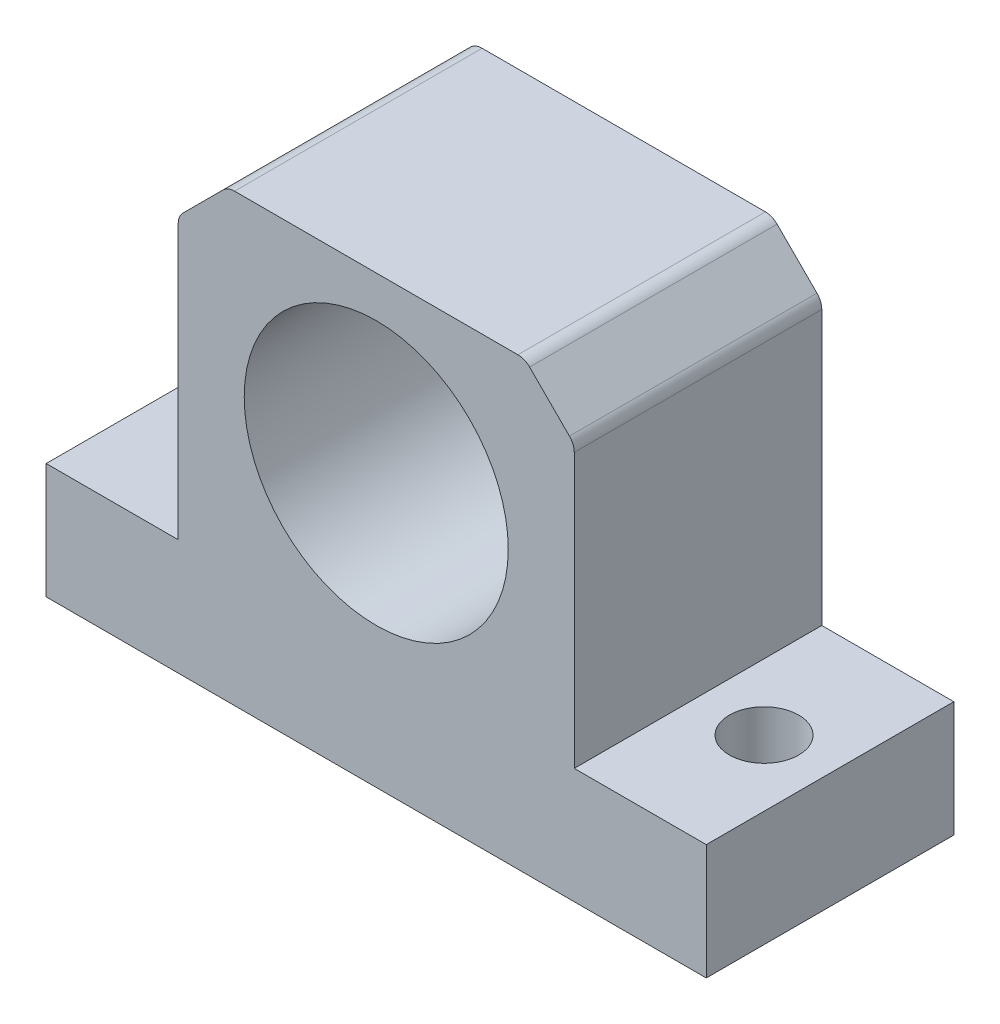
SolidWorks part; units mm, degrees
ref_plane "Front Plane" through (0, 0, 0) normal (0, 0, 1) x (1, 0, 0)
ref_plane "Top Plane" through (0, 0, 0) normal (0, 1, 0) x (1, 0, 0)
ref_plane "Right Plane" through (0, 0, 0) normal (1, 0, 0) x (0, 0, -1)
sketch "Sketch1" plane through (0, 0, 0) normal (0, 0, 1) x (1, 0, 0)
  line L0 (0, 0) -> (0, 34.3831) construction
  line L1 (0, 0) -> (-31.759, 0) construction
  line L2 (20, 0) -> (-20, 0)
  line L3 (-20, 0) -> (-20, 7)
  line L4 (-20, 7) -> (-12, 7)
  line L5 (-12, 7) -> (-12, 27)
  line L6 (-12, 27) -> (12, 27)
  line L7 (20, 0) -> (20, 7)
  line L8 (20, 7) -> (12, 7)
  line L9 (12, 7) -> (12, 27)
  circle A0 centre (0, 16.5) radius 8
  point P15 (0, 27)
  dimension "D1" = 16
  dimension "D2" = 16.5
  dimension "D3" = 20
  dimension "D4" = 7
  dimension "D5" = 8
  dimension "D6" = 27
extrude "Boss-Extrude1" add sketch "Sketch1" along normal blind 15
chamfer "Chamfer1" distance 3 angle 45 2 edges at (-12, 27, 7.5) (12, 27, 7.5)
sketch "Sketch2" plane through (0, 0, 0) normal (0, 0, -1) x (-1, 0, 0)
  circle A0 centre (0, 16.5) radius 5
  circle A1 centre (0, 16.5) radius 8 construction
  circle A2 centre (0, 16.5) radius 8
  dimension "D1" = 10
extrude "Boss-Extrude2" add sketch "Sketch2" against normal blind 3
sketch "Sketch3" plane through (0, 0, 0) normal (0, -1, 0) x (1, 0, 0)
  line L0 (0, 0) -> (0, 15) construction
  line L1 (-20, 15) -> (20, 15) construction
  line L2 (-20, 7.5) -> (20, 7.5) construction
  line L3 (-20, 15) -> (-20, 0) construction
  line L4 (20, 15) -> (20, 0) construction
  circle A0 centre (16, 7.5) radius 2.196
  circle A1 centre (-16, 7.5) radius 2.196
  dimension "D1" = 4
hole_wizard "M5 Tapped Hole1" positions "3DSketch1" profile "Sketch4" tap size "M5" standard "GB"
sketch3d "3DSketch1"
  point P0 (-16, 0, 7.5)
  point P3 (16, 0, 7.5)
sketch "Sketch4" plane through (-16, 0, 7.5) normal (1, 0, 0) x (0, 0, -1)
  line L0 (0, 0) -> (0, 104.8218)
  line L1 (0, 104.8218) -> (2.1, 103.56)
  line L2 (2.1, 103.56) -> (2.1, 0)
  line L5 (2.1, 0) -> (0, 0)
  line L10 (0, 104.8218) -> (-2.1, 103.56) construction
  line L11 (0, -6.35) -> (0, 107.95) construction
  dimension "Tap Drill Dia." = 4.2
  dimension "Tap Drill Depth" = 103.56
  dimension "Drill Angle" = 118
cosmetic thread "Hole Thread1" parameters "D1"=7, "D2"=5
cosmetic thread "Hole Thread2" parameters "D1"=7, "D2"=5
fillet "Fillet1" radius 1 4 edges at (-12, 24, 7.5) (-9, 27, 7.5) (9, 27, 7.5) (12, 24, 7.5)
